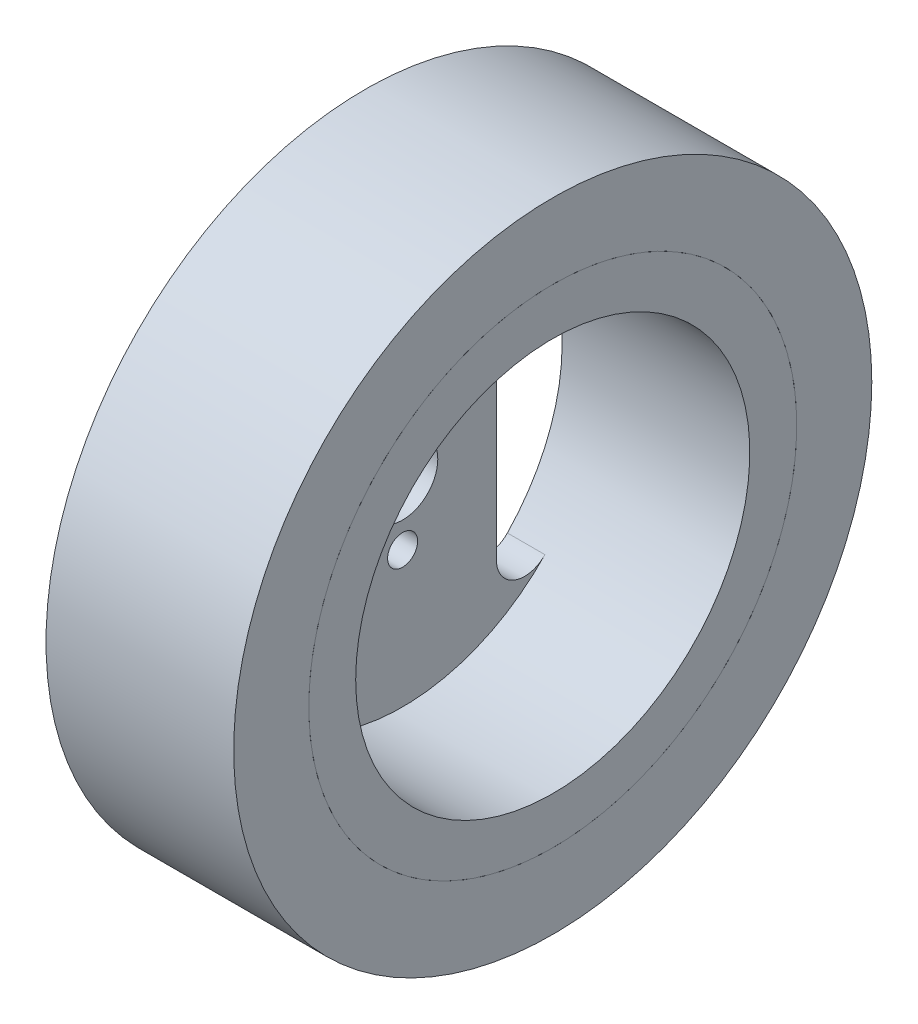
SolidWorks part; units mm, degrees
material "6061 合金"
ref_plane "前视基准面" through (0, 0, 0) normal (0, 0, 1) x (1, 0, 0)
ref_plane "上视基准面" through (0, 0, 0) normal (0, 1, 0) x (1, 0, 0)
ref_plane "右视基准面" through (0, 0, 0) normal (1, 0, 0) x (0, 0, -1)
sketch "草图1" plane through (0, 0, 0) normal (0, 0, 1) x (1, 0, 0)
  line L0 (0, 0) -> (65.3556, 0) construction
  line L1 (0, 0) -> (0, 26)
  line L2 (0, 26) -> (20, 26)
  line L3 (20, 26) -> (20, 21)
  line L4 (20, 21) -> (4, 21)
  line L5 (4, 21) -> (4, 0)
  line L6 (4, 0) -> (0, 0)
  dimension "D1" = 21
  dimension "D2" = 20
  dimension "D3" = 4
  dimension "D4" = 5
revolve "旋转1" add sketch "草图1" angle 360 about L0
sketch "草图2" plane through (4, 0, 0) normal (1, 0, 0) x (0, 0, -1)
  line L0 (-10, 12.4499) -> (-10, -12.4499)
  line L1 (0, 0) -> (0, 21) construction
  line L2 (10, 12.4499) -> (10, -12.4499)
  circle A0 centre (0, 0) radius 3.75
  circle A1 centre (0, 0) radius 6.5 construction
  arc A2 (-15.1667, 14.5249) -> (-15.1667, -14.5249) centre (0, 0) ccw
  arc A3 (15.1667, -14.5249) -> (15.1667, 14.5249) centre (0, 0) ccw
  circle A4 centre (0, 6.5) radius 1.6
  circle A5 centre (0, -6.5) radius 1.6
  arc A6 (10, -12.4499) -> (15.1667, -14.5249) centre (13, -12.4499) ccw
  arc A7 (10, 12.4499) -> (15.1667, 14.5249) centre (13, 12.4499) cw
  arc A8 (-10, 12.4499) -> (-15.1667, 14.5249) centre (-13, 12.4499) ccw
  arc A9 (-10, -12.4499) -> (-15.1667, -14.5249) centre (-13, -12.4499) cw
  point P15 (10, -18.4662)
  point P18 (10, 18.4662)
  point P21 (-10, 18.4662)
  point P24 (-10, -18.4662)
  dimension "D1" = 7.5
  dimension "D2" = 13
  dimension "D3" = 3.2
  dimension "D4" = 3.2
  dimension "D5" = 10
  dimension "D6" = 42
  dimension "D7" = 3
extrude "切除-拉伸1" cut sketch "草图2" against normal blind 10
sketch "草图3" plane through (20, 0, 0) normal (1, 0, 0) x (0, 0, -1)
  circle A0 centre (0, 0) radius 34
  circle A1 centre (0, 0) radius 26 construction
  circle A2 centre (0, 0) radius 26
  dimension "D1" = 68
extrude "凸台-拉伸1" add sketch "草图3" against normal up to surface (20 mm away) separate body up to face at (0, 0, 13.691)
